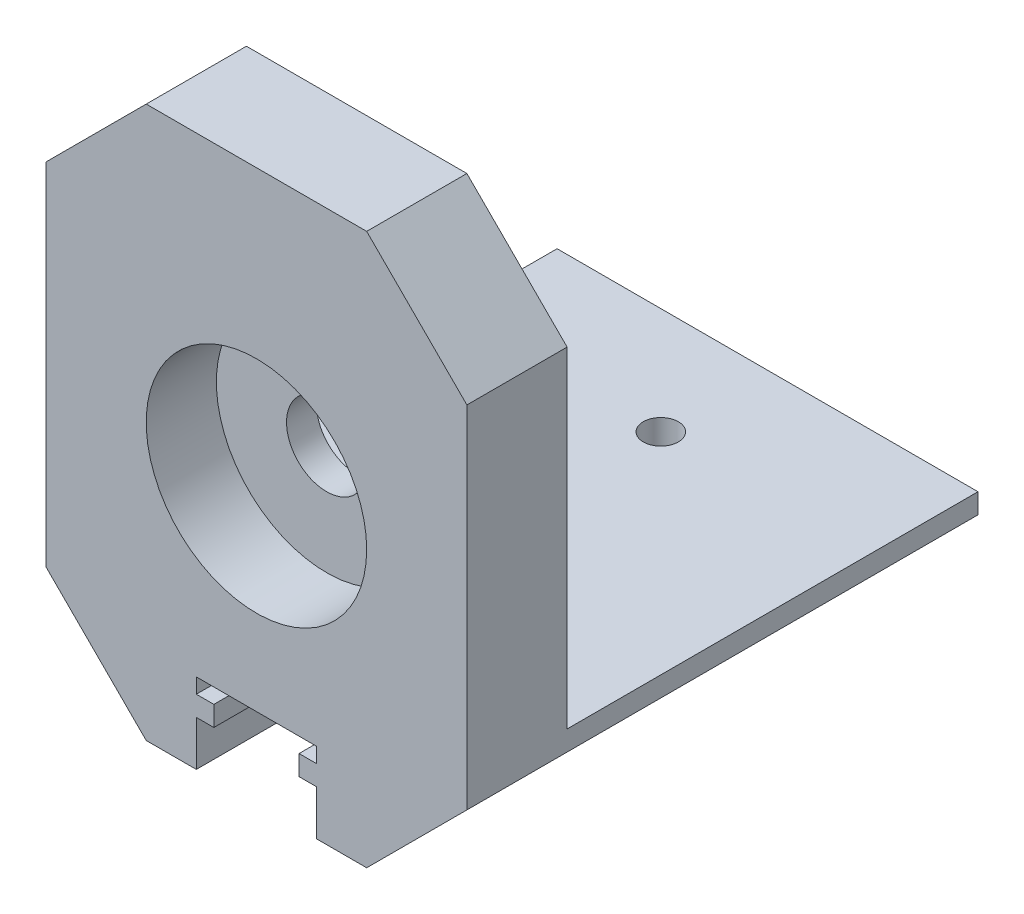
SolidWorks part; units mm, degrees
material "PLA"
ref_plane "Piano frontale" through (0, 0, 0) normal (0, 0, 1) x (1, 0, 0)
ref_plane "Piano superiore" through (0, 0, 0) normal (0, 1, 0) x (1, 0, 0)
ref_plane "Piano destro" through (0, 0, 0) normal (1, 0, 0) x (0, 0, -1)
sketch "Schizzo1" plane through (0, 0, 0) normal (0, 0, 1) x (1, 0, 0)
  line L0 (6, -23) -> (6, -27.5)
  line L1 (-21, -27.5) -> (-6, -27.5)
  line L2 (-21, -27.5) -> (-21, 27.5)
  line L3 (-21, 27.5) -> (21, 27.5)
  line L4 (21, -27.5) -> (21, 27.5)
  line L5 (-21, -27.5) -> (21, 27.5) construction
  line L6 (-21, 27.5) -> (21, -27.5) construction
  line L7 (6, -19.5) -> (6, -21)
  line L8 (6, -19.5) -> (-6, -19.5)
  line L9 (-6, -19.5) -> (-6, -21)
  line L11 (6, -19.5) -> (-6, -27.5) construction
  line L12 (-6, -19.5) -> (6, -27.5) construction
  line L13 (6, -21) -> (4.25, -21)
  line L14 (4.25, -21) -> (4.25, -23)
  line L15 (6, -23) -> (4.25, -23)
  line L16 (-6, -21) -> (-4.25, -21)
  line L17 (-4.25, -21) -> (-4.25, -23)
  line L18 (-6, -23) -> (-4.25, -23)
  line L19 (-6, -23) -> (-6, -27.5)
  line L20 (6, -27.5) -> (21, -27.5)
  point P0 (0, 0)
  point P6 (0, -23.5)
  dimension "D1" = 42
  dimension "D2" = 55
  dimension "D3" = 12
  dimension "D4" = 8
  dimension "D5" = 2
  dimension "D6" = 2
  dimension "D7" = 1.5
  dimension "D8" = 1.5
  dimension "D9" = 8.5
  dimension "D10" = 4.25
extrude "Estrusione-Estrusione1" add sketch "Schizzo1" along normal blind 10
sketch "Schizzo2" plane through (0, 0, 10) normal (0, 0, 1) x (1, 0, 0)
  circle A0 centre (0, 0) radius 11
  dimension "D1" = 22
extrude "Taglio-Estrusione1" cut sketch "Schizzo2" against normal blind 7
sketch "Schizzo3" plane through (0, 0, 3) normal (0, 0, 1) x (1, 0, 0)
  circle A0 centre (0, 0) radius 4
  dimension "D1" = 8
extrude "Taglio-Estrusione2" cut sketch "Schizzo3" against normal through all
sketch "Schizzo4" plane through (0, 0, 0) normal (0, 0, -1) x (-1, 0, 0)
  line L0 (-21, -27.5) -> (-6, -27.5)
  line L1 (-6, -27.5) -> (-21, -27.5) construction
  line L2 (-6, -27.5) -> (-6, -23)
  line L3 (-6, -23) -> (-4.25, -23)
  line L4 (-4.25, -23) -> (-4.25, -21)
  line L5 (-4.25, -21) -> (-6, -21)
  line L8 (-21, -27.5) -> (-21, -15.5)
  line L9 (-21, -27.5) -> (-21, 27.5) construction
  line L11 (-21, -15.5) -> (21, -15.5)
  line L12 (0, -15.5) -> (0, 0) construction
  line L13 (-6, -21) -> (-6, -19.5)
  line L14 (-6, -19.5) -> (6, -19.5)
  line L15 (6, -19.5) -> (-6, -19.5) construction
  line L16 (6, -21) -> (6, -19.5)
  line L17 (21, -27.5) -> (21, -15.5)
  line L18 (4.25, -21) -> (6, -21)
  line L19 (4.25, -23) -> (4.25, -21)
  line L20 (6, -23) -> (4.25, -23)
  line L21 (6, -27.5) -> (6, -23)
  line L22 (21, -27.5) -> (6, -27.5)
  point P25 (0, -19.5)
  dimension "D1" = 5.5
extrude "Estrusione-Estrusione2" add sketch "Schizzo4" along normal blind 41
chamfer "Smusso1" distance 10 angle 45 4 edges at (-21, 27.5, 5) (21, 27.5, 5) (-21, -27.5, -15.5) (21, -27.5, -15.5)
sketch "Schizzo5" plane through (0, -15.5, 0) normal (0, 1, 0) x (1, 0, 0)
  line L0 (0, 41) -> (0, 0) construction
  line L1 (-21, 41) -> (21, 41) construction
  circle A0 centre (0, 30.35) radius 1.75
  circle A1 centre (0, 5.35) radius 1.75
  dimension "D1" = 3.5
  dimension "D3" = 3.5
  dimension "D2" = 10.65
  dimension "D4" = 25
extrude "Taglio-Estrusione3" cut sketch "Schizzo5" against normal through all
